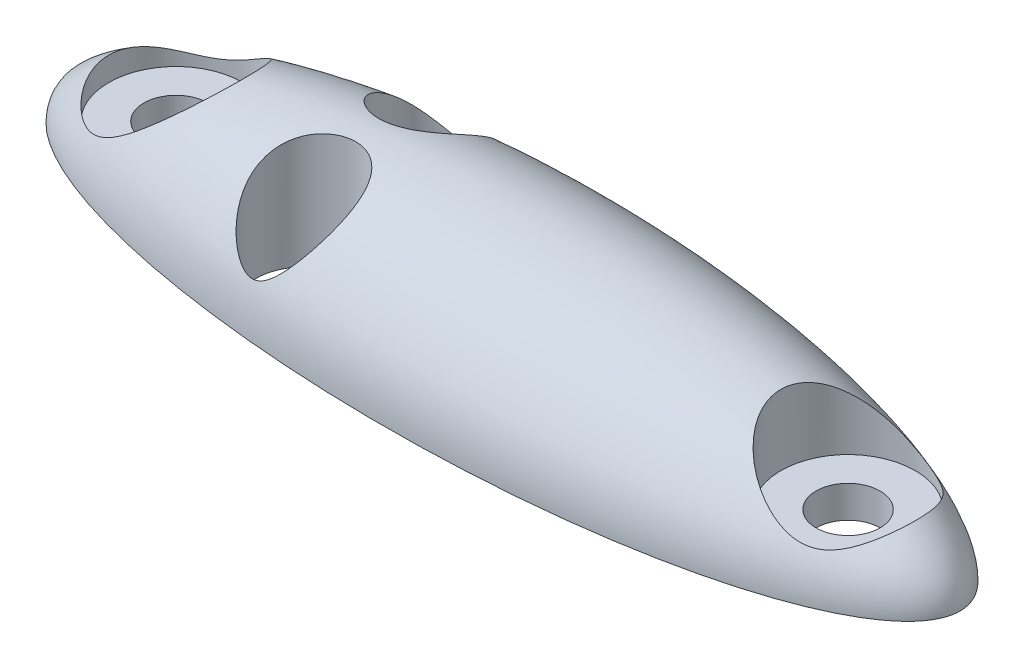
SolidWorks part; units mm, degrees
ref_plane "Front Plane" through (0, 0, 0) normal (0, 0, 1) x (1, 0, 0)
ref_plane "Top Plane" through (0, 0, 0) normal (0, 1, 0) x (1, 0, 0)
ref_plane "Right Plane" through (0, 0, 0) normal (1, 0, 0) x (0, 0, -1)
sketch "Sketch1" plane through (0, 0, 0) normal (0, 0, 1) x (1, 0, 0)
  line L0 (-14, 0) -> (14, 0) construction
  line L1 (-14, 0) -> (14, 0)
  circle A0 centre (-10.75, 0) radius 1 construction
  circle A1 centre (10.75, 0) radius 1 construction
  ellipse E0 centre (0, 0) end of major axis (14, 0) minor radius 4 (14, 0) -> (-14, 0) ccw
  dimension "D3" = 2
  dimension "D1" = 14
  dimension "D2" = 4
  dimension "D4" = 3.25
  dimension "D5" = 3.25
revolve "Revolve1" add sketch "Sketch1" angle 360 about L0
sketch "Sketch2" plane through (0, 0, 0) normal (0, 0, 1) x (1, 0, 0)
  line L1 (-26.9158, 0) -> (23.719, 0)
  line L2 (-26.9158, 0) -> (-26.9158, -13.0728)
  line L3 (-26.9158, -13.0728) -> (23.719, -13.0728)
  line L4 (23.719, 0) -> (23.719, -13.0728)
  point P4 (10.3338, 0)
  point P5 (-26.9158, -9.0163)
  point P6 (23.719, -13.0728)
extrude "Cut-Extrude1" cut sketch "Sketch2" against normal through all both and the other way through all
sketch "Sketch3" plane through (0, 0, 0) normal (0, -1, 0) x (1, 0, 0)
  line L0 (-14, 0) -> (14, 0) construction
  circle A0 centre (-10.5, 0) radius 1
  circle A1 centre (10.5, 0) radius 1
  ellipse E0 centre (0, 0) end of major axis (14, 0) minor radius 4 (-14, 0) -> (14, 0) ccw construction
  ellipse E1 centre (0, 0) end of major axis (14, 0) minor radius 4 (14, 0) -> (-14, 0) ccw construction
  dimension "D1" = 2
  dimension "D2" = 3.5
  dimension "D3" = 3.5
extrude "Cut-Extrude2" cut sketch "Sketch3" against normal through all
ref_plane "Plane1" through (0, 1, 0) normal (0, -1, 0) x (-1, 0, 0)
sketch "Sketch4" plane through (0, 1, 0) normal (0, -1, 0) x (-1, 0, 0)
  circle A0 centre (10.5, 0) radius 2.1
  circle A1 centre (-10.5, 0) radius 2.1
  dimension "D1" = 4.2
extrude "Cut-Extrude3" cut sketch "Sketch4" against normal through all
sketch "Sketch5" plane through (0, 0, 0) normal (0, -1, 0) x (1, 0, 0)
  line L0 (-10.5, 0) -> (10.5, 0) construction
  line L1 (-4.5, 2) -> (-4.5, -2) construction
  circle A0 centre (-4.5, 2) radius 1.5
  circle A1 centre (-4.5, -2) radius 1.5
  point P8 (-4.5, 0)
  dimension "D1" = 3
  dimension "D2" = 4
  dimension "D3" = 4.5
extrude "Cut-Extrude4" cut sketch "Sketch5" against normal through all
